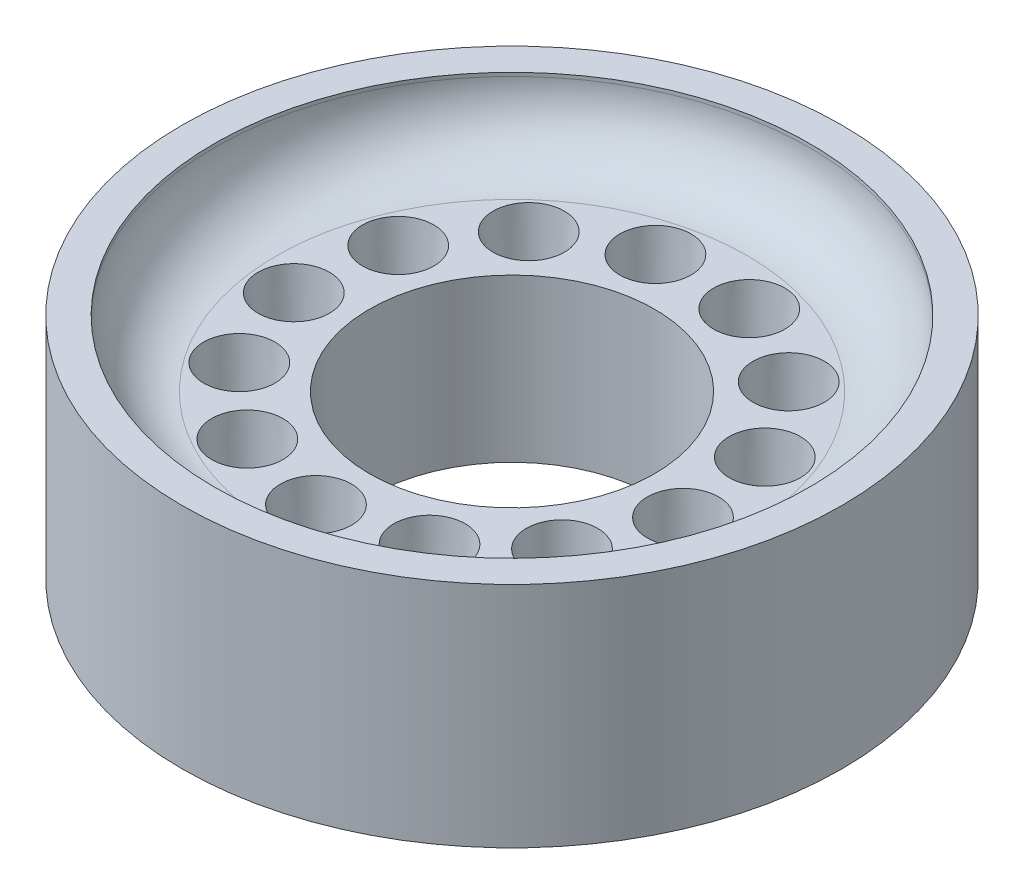
SolidWorks part; units mm, degrees
ref_plane "Front Plane" through (0, 0, 0) normal (0, 0, 1) x (1, 0, 0)
ref_plane "Top Plane" through (0, 0, 0) normal (0, 1, 0) x (1, 0, 0)
ref_plane "Right Plane" through (0, 0, 0) normal (1, 0, 0) x (0, 0, -1)
sketch "Sketch1" plane through (0, 0, 0) normal (0, 1, 0) x (1, 0, 0)
  line L0 (0, 0) -> (0, 9.3155) construction
  circle A0 centre (0, 0) radius 5.5 construction
  circle A2 centre (0, 0) radius 9.25
  circle A15 centre (0, 0) radius 4
  point P33 (0, 0)
  dimension "D1" = 5.5
  dimension "D3" = 18.5
  dimension "D5" = 8
extrude "Boss-Extrude1" add sketch "Sketch1" along normal blind 6.4
sketch "Sketch2" plane through (0, 6.4, 0) normal (0, 1, 0) x (1, 0, 0)
  circle A0 centre (0, 0) radius 8.35
  circle A1 centre (0, 0) radius 9.25 construction
  dimension "D1" = 0.9
extrude "Cut-Extrude1" cut sketch "Sketch2" against normal blind 1.85
fillet "Fillet1" radius 1.75 1 edges at (0, 4.55, 8.35)
sketch "Sketch3" plane through (0, 4.55, 0) normal (0, 1, 0) x (1, 0, 0)
  circle A0 centre (0, -5.5) radius 1
  circle A1 centre (0, 0) radius 5.5 construction
  dimension "D1" = 2
extrude "Cut-Extrude2" cut sketch "Sketch3" against normal up to next (4.55 mm away) draft 5
pattern_circular "CirPattern1" count 13 over 360 about axis through (0, 0, 0) along (0, 1, 0) of "Cut-Extrude2"
